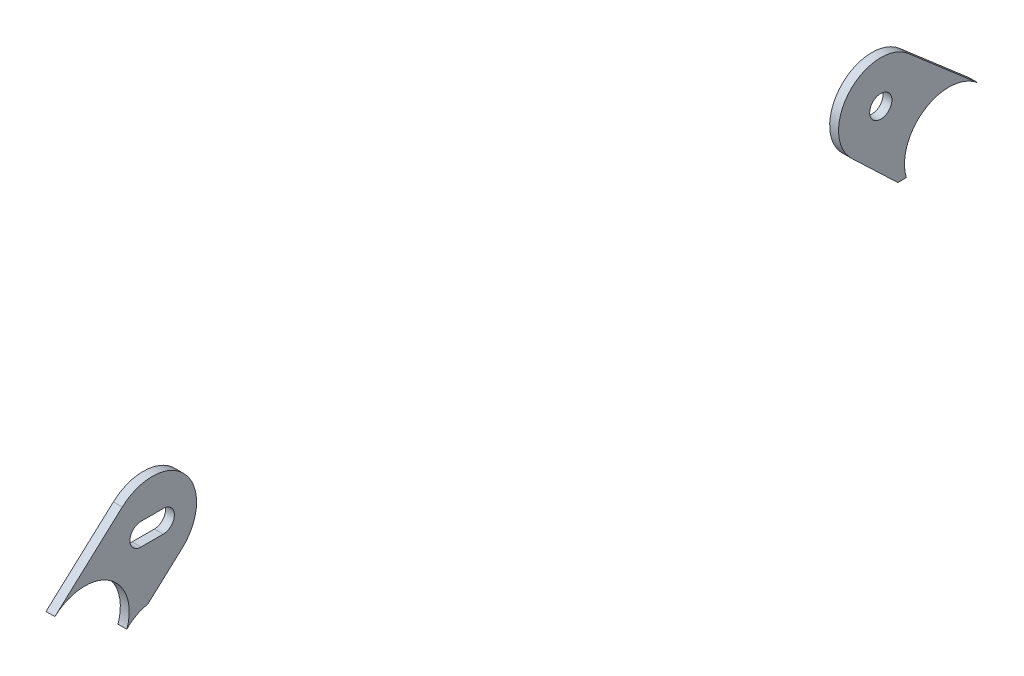
SolidWorks part; units mm, degrees
material "AISI 4130 Steel, normalized at 870C"
ref_plane "Front" through (0, 0, 0) normal (0, 0, 1) x (1, 0, 0)
ref_plane "Top" through (0, 0, 0) normal (0, 1, 0) x (1, 0, 0)
ref_plane "Right" through (0, 0, 0) normal (1, 0, 0) x (0, 0, -1)
sketch "Sketch1" plane through (0, 0, 0) normal (1, 0, 0) x (0, 0, -1)
  line L0 (-132.1732, -84.5824) -> (-112.919, -67.08)
  line L1 (-115.0881, -103.3776) -> (-95.8339, -85.8752)
  line L2 (111.7527, -67.172) -> (131.6483, -84.3726)
  line L3 (95.5401, -85.0345) -> (114.5825, -103.1753)
  line L5 (-107.5514, -79.6526) -> (-101.2014, -79.6526)
  line L6 (-107.5514, -79.6526) -> (-107.5514, -73.3026) construction
  line L7 (-107.5514, -73.3026) -> (-101.2014, -73.3026)
  line L8 (-101.2014, -79.6526) -> (-101.2014, -73.3026) construction
  line L9 (-107.5514, -79.6526) -> (-101.2014, -73.3026) construction
  line L10 (-107.5514, -73.3026) -> (-101.2014, -79.6526) construction
  arc A4 (-95.8339, -85.8752) -> (-112.919, -67.08) centre (-104.3764, -76.4776) ccw
  arc A5 (95.5401, -85.0345) -> (111.7527, -67.172) centre (103.862, -76.299) cw
  arc A6 (114.5825, -103.1753) -> (131.6483, -84.3726) centre (123.3424, -93.98) cw
  arc A7 (-132.1732, -84.5824) -> (-115.0881, -103.3776) centre (-123.6307, -93.98) cw
  circle A8 centre (-104.3764, -76.4776) radius 3.175 construction
  circle A9 centre (103.862, -76.299) radius 3.175
  arc A10 (-101.2014, -73.3026) -> (-101.2014, -79.6526) centre (-101.2014, -76.4776) cw
  arc A11 (-107.5514, -73.3026) -> (-107.5514, -79.6526) centre (-107.5514, -76.4776) ccw
  dimension "D1" = 6.35
  dimension "D2" = 6.35
  dimension "D3" = 3.175
  dimension "D4" = 12.7
extrude "Boss-Extrude1" add sketch "Sketch1" along normal blind 2.54 contours L0 A7 L1 A4 A11 L7 A10 L5 | L3 A6 L2 A5 A9
sketch "Sketch4" plane through (2.54, 0, 0) normal (1, 0, 0) x (0, 0, -1)
  line L0 (111.168, -97.5957) -> (108.628, -97.5957)
  line L1 (111.168, -97.5957) -> (108.628, -97.5957)
  line L2 (108.628, -97.5957) -> (102.1475, -97.5957)
  line L3 (102.1475, -97.5957) -> (102.1475, -107.3142)
  line L4 (102.1475, -107.3142) -> (125.3219, -107.3142)
  line L5 (125.3219, -107.3142) -> (121.6983, -97.5957)
  line L6 (121.6983, -97.5957) -> (111.168, -97.5957)
extrude "Cut-Extrude1" cut sketch "Sketch4" against normal blind 10
sketch "Sketch5" plane through (2.54, 0, 0) normal (1, 0, 0) x (0, 0, -1)
  line L0 (-111.5893, -98.0167) -> (-113.4031, -101.509)
  spline S0 degree 3 poles (-111.5893, -98.0167) (-96.8618, -81.2669) (-67.0962, -98.6452) (-77.1981, -118.0956) (-87.3, -137.546) (-118.6355, -123.1903) (-113.4031, -101.509) knots 0 0 0 0 0.5 0.5 0.5 1 1 1 1 weights 1 0.385133 0.385133 1 0.385133 0.385133 1
  spline S1 degree 3 poles (-111.5893, -98.0167) (-96.8618, -81.2669) (-67.0962, -98.6452) (-77.1981, -118.0956) (-87.3, -137.546) (-118.6355, -123.1903) (-113.4031, -101.509) knots 0 0 0 0 0.5 0.5 0.5 1 1 1 1 weights 1 0.385133 0.385133 1 0.385133 0.385133 1
extrude "Cut-Extrude2" cut sketch "Sketch5" against normal blind 10
